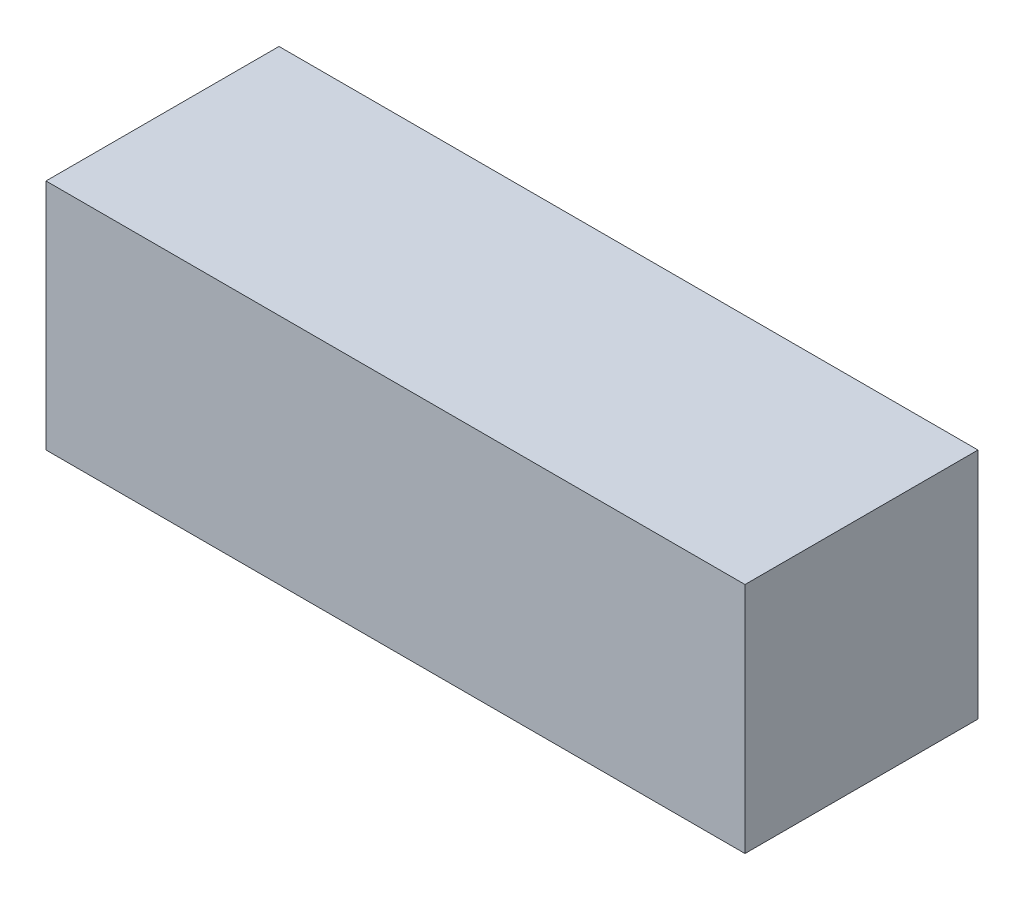
SolidWorks part; units mm, degrees
ref_plane "Front Plane" through (0, 0, 0) normal (0, 0, 1) x (1, 0, 0)
ref_plane "Top Plane" through (0, 0, 0) normal (0, 1, 0) x (1, 0, 0)
ref_plane "Right Plane" through (0, 0, 0) normal (1, 0, 0) x (0, 0, -1)
sketch "Sketch2" plane through (0, 0, 0) normal (0, 0, 1) x (1, 0, 0)
  line L1 (0, 0) -> (300, 0)
  line L2 (0, 0) -> (0, 100)
  line L3 (0, 100) -> (300, 100)
  line L4 (300, 0) -> (300, 100)
  dimension "D1" = 300
  dimension "D2" = 100
extrude "Boss-Extrude1" add sketch "Sketch2" along normal blind 100
